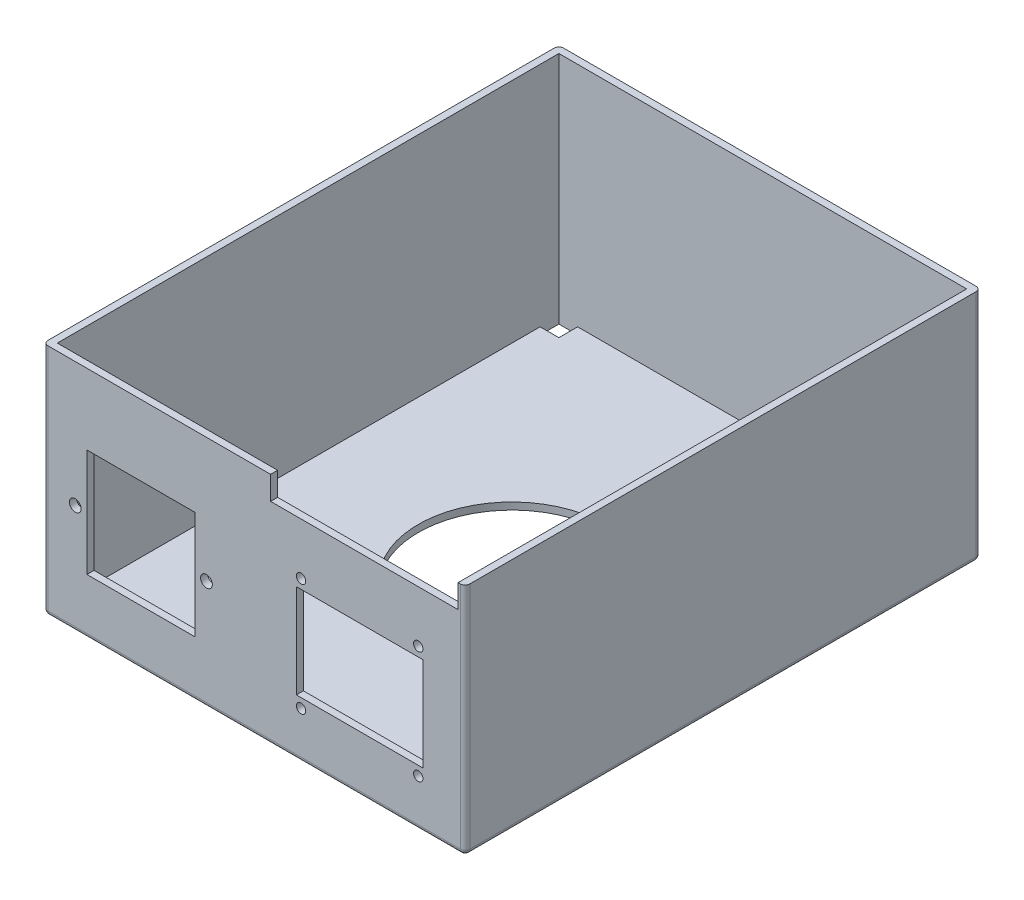
SolidWorks part; units mm, degrees
ref_plane "前视基准面" through (0, 0, 0) normal (0, 0, 1) x (1, 0, 0)
ref_plane "上视基准面" through (0, 0, 0) normal (0, 1, 0) x (1, 0, 0)
ref_plane "右视基准面" through (0, 0, 0) normal (1, 0, 0) x (0, 0, -1)
sketch "草图4" plane through (0, 0, 0) normal (0, 1, 0) x (1, 0, 0)
  line L1 (45, -55) -> (-45, -55)
  line L2 (45, -55) -> (45, 55)
  line L3 (45, 55) -> (-45, 55)
  line L4 (-45, -55) -> (-45, 55)
  line L5 (45, -55) -> (-45, 55) construction
  line L6 (45, 55) -> (-45, -55) construction
  point P0 (0, 0)
  dimension "D1" = 110
  dimension "D2" = 90
extrude "凸台-拉伸2" add sketch "草图4" along normal blind 50
shell "抽壳2" thickness 1.5
sketch "草图5" plane through (0, 1.5, 0) normal (0, 1, 0) x (1, 0, 0)
  line L1 (-43.5, 53.5) -> (-39.5, 53.5)
  line L2 (-43.5, 53.5) -> (-43.5, 49.5)
  line L3 (-43.5, 49.5) -> (-39.5, 49.5)
  line L4 (-39.5, 53.5) -> (-39.5, 49.5)
  dimension "D1" = 4
  dimension "D2" = 4
extrude "切除-拉伸2" cut sketch "草图5" against normal blind 50
mirror "镜向4" about plane through (0, 0, 0) normal (0, 0, 1) of "切除-拉伸2"
mirror "镜向5" about plane through (0, 0, 0) normal (1, 0, 0) of "镜向4", "切除-拉伸2"
sketch "草图9" plane through (0, 1.5, 0) normal (0, 1, 0) x (1, 0, 0)
  circle A0 centre (0, 0) radius 20
  dimension "D1" = 40
extrude "切除-拉伸5" cut sketch "草图9" against normal blind 50
sketch "草图12" plane through (0, 0, 55) normal (0, 0, 1) x (1, 0, 0)
  line L1 (-35.6771, 34.9103) -> (-12.6771, 34.9103)
  line L2 (-35.6771, 34.9103) -> (-35.6771, 11.9103)
  line L3 (-35.6771, 11.9103) -> (-12.6771, 11.9103)
  line L4 (-12.6771, 34.9103) -> (-12.6771, 11.9103)
  dimension "D1" = 23
  dimension "D2" = 23
extrude "切除-拉伸6" cut sketch "草图12" against normal blind 50
sketch "草图15" plane through (0, 0, -53.5) normal (0, 0, 1) x (1, 0, 0)
  line L0 (-35.6771, 23.4103) -> (-12.6771, 23.4103) construction
  line L2 (-35.6771, 34.9103) -> (-35.6771, 11.9103) construction
  line L3 (-12.6771, 11.9103) -> (-12.6771, 34.9103) construction
  line L4 (-12.6771, 23.4103) -> (-10.1771, 23.4103) construction
  line L5 (-35.6771, 23.4103) -> (-38.1771, 23.4103) construction
  circle A0 centre (-10.1771, 23.4103) radius 1.25
  circle A1 centre (-38.1771, 23.4103) radius 1.25
  dimension "D2" = 2.5
  dimension "D4" = 2.5
  dimension "D1" = 2.5
  dimension "D3" = 2.5
extrude "切除-拉伸8" cut sketch "草图15" along normal blind 129
sketch "草图16" plane through (0, 0, 55) normal (0, 0, 1) x (1, 0, 0)
  line L1 (36, 12) -> (9, 12)
  line L2 (36, 12) -> (36, 32)
  line L3 (36, 32) -> (9, 32)
  line L4 (9, 12) -> (9, 32)
  line L5 (-45, 0) -> (45, 0) construction
  line L8 (45, 50) -> (45, 0) construction
  point P12 (45, 25)
  dimension "D1" = 27
  dimension "D2" = 20
  dimension "D3" = 12
  dimension "D4" = 9
extrude "切除-拉伸9" cut sketch "草图16" against normal blind 50
sketch "草图17" plane through (0, 0, 55) normal (0, 0, 1) x (1, 0, 0)
  line L0 (36, 32) -> (36, 51.88) construction
  line L1 (36, 32) -> (9, 32) construction
  circle A0 centre (35, 34) radius 1
  point P9 (36, 33.866)
  dimension "D1" = 2
  dimension "D2" = 2
  dimension "D3" = 1
extrude "切除-拉伸10" cut sketch "草图17" against normal blind 50
sketch "草图19" plane through (0, 0, 55) normal (0, 0, 1) x (1, 0, 0)
  line L0 (36, 12) -> (36, 0) construction
  line L1 (-45, 0) -> (45, 0) construction
  line L2 (9, 12) -> (36, 12) construction
  circle A0 centre (35, 10) radius 1
  point P7 (0, 0)
  point P12 (36, 9.5262)
  dimension "D1" = 2
  dimension "D2" = 2
  dimension "D3" = 1
extrude "切除-拉伸11" cut sketch "草图19" against normal blind 50
sketch "草图20" plane through (0, 0, -53.5) normal (0, 0, 1) x (1, 0, 0)
  line L0 (9, 32) -> (9, 42.0666) construction
  point P3 (0, 0)
sketch "草图21" plane through (0, 0, 55) normal (0, 0, 1) x (1, 0, 0)
  line L0 (36, 32) -> (9, 32) construction
  line L1 (9, 32) -> (9, 42.0666) construction
  circle A0 centre (10, 34) radius 1
  point P2 (0, 0)
  dimension "D1" = 2
  dimension "D2" = 2
  dimension "D3" = 1
extrude "切除-拉伸12" cut sketch "草图21" against normal blind 50
sketch "草图22" plane through (0, 0, 55) normal (0, 0, 1) x (1, 0, 0)
  line L0 (9, 12) -> (9, 2.8225) construction
  line L1 (9, 12) -> (36, 12) construction
  circle A0 centre (10, 10) radius 1
  point P5 (0, 0)
  point P8 (0, 0)
  point P11 (9, 10.4676)
  dimension "D1" = 2
  dimension "D2" = 2
  dimension "D3" = 1
extrude "切除-拉伸13" cut sketch "草图22" against normal blind 50
fillet "圆角1" radius 1 4 edges at (45, 25, -55) (-45, 25, -55) (-45, 25, 55) (45, 25, 55)
fillet "圆角2" radius 1 8 edges at (-44.7071, 0, 54.7071) (-45, 0, 0) (-44.7071, 0, -54.7071) (0, 0, -55) (44.7071, 0, -54.7071) (45, 0, 0) (44.7071, 0, 54.7071) (0, 0, 55)
sketch "草图23" plane through (0, 0, -53.5) normal (0, 0, 1) x (1, 0, 0)
  line L0 (-34.5025, 11.9103) -> (-53.4422, 11.9103) construction
  line L1 (-35.6771, 11.9103) -> (-12.6771, 11.9103) construction
  point P4 (-43.018, 5.9869)
sketch "草图24" plane through (0, 0, 55) normal (0, 0, 1) x (1, 0, 0)
  line L0 (-31.4193, 1) -> (-54.6168, 1) construction
  line L1 (-44, 1) -> (44, 1) construction
  line L5 (44, 50) -> (4, 50)
  line L6 (44, 50) -> (44, 45)
  line L7 (44, 45) -> (4, 45)
  line L8 (4, 50) -> (4, 45)
  dimension "D1" = 40
  dimension "D2" = 5
sketch "草图25" plane through (0, 0, 53.5) normal (0, 0, -1) x (-1, 0, 0)
  line L1 (-43.5, 50) -> (-3.5, 50)
  line L2 (-43.5, 50) -> (-43.5, 45)
  line L3 (-43.5, 45) -> (-3.5, 45)
  line L4 (-3.5, 50) -> (-3.5, 45)
  dimension "D1" = 40
  dimension "D2" = 5
extrude "切除-拉伸15" cut sketch "草图25" against normal blind 50
